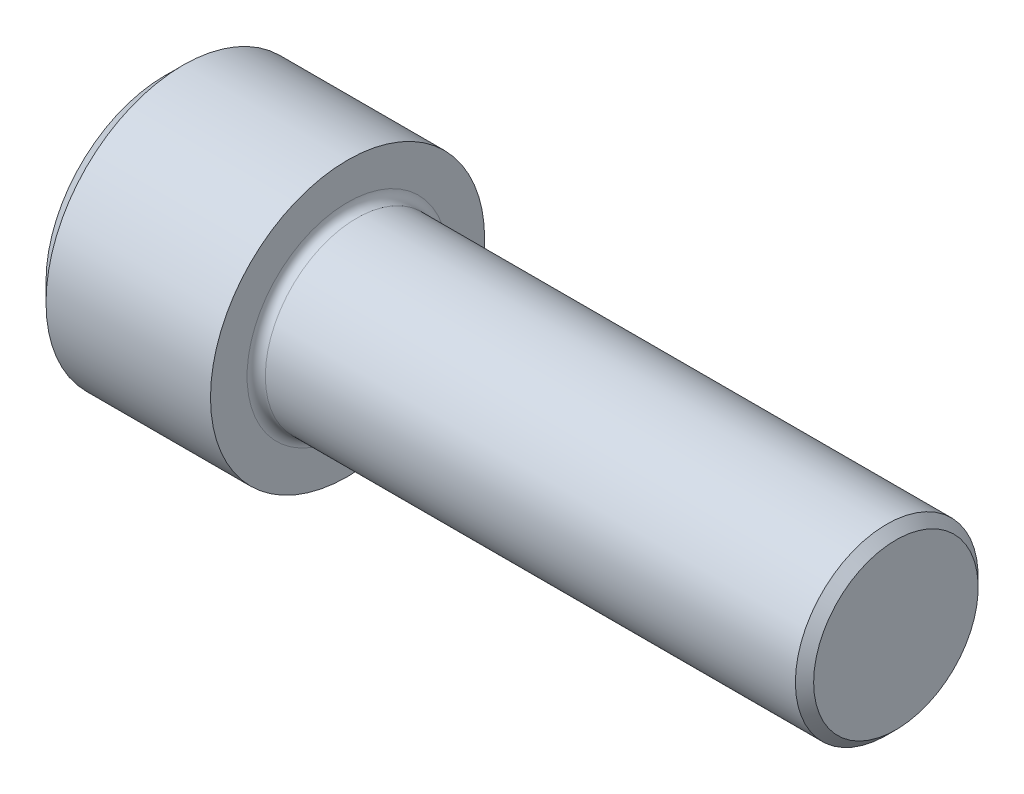
SolidWorks part; units mm, degrees
revolve "Base-Revolve" add sketch "BodySke"
sketch "BodySke" plane through (0, 0, 0) normal (0, 0, 1) x (1, 0, 0)
  line L0 (0, 0) -> (0, 16.51)
  line L1 (2.54, 19.05) -> (25.4, 19.05)
  line L2 (25.4, 19.05) -> (25.4, 12.7)
  line L3 (25.4, 12.7) -> (100.3313, 12.7)
  line L4 (101.6, 11.4313) -> (101.6, 0)
  line L5 (101.6, 0) -> (0, 0)
  line L6 (-31.75, 0) -> (127, 0) construction
  line L7 (0, 16.51) -> (2.54, 19.05)
  line L8 (101.6, 11.4313) -> (100.3313, 12.7)
  line L9 (0, -16.51) -> (2.54, -19.05) construction
  line L10 (101.6, -11.4313) -> (100.3313, -12.7) construction
  line L11 (27.5167, 9.525) -> (27.5167, 3.175) construction
  line L12 (63.5, 9.525) -> (63.5, 3.175) construction
  line L13 (63.5, 9.525) -> (63.5, 3.175) construction
  dimension "Diameter" = 25.4
  dimension "Head_ht" = 25.4
  dimension "Length" = 76.2
  dimension "Body_ch_ang" = 45
  dimension "Head_dia" = 38.1
  dimension "Head_ch_ang" = 45
  dimension "Head_side_ht" = 22.86
  dimension "Minor_dia" = 22.8625
  dimension "Advance" = 2.1167
  dimension "Thread_nom" = 38.1
  dimension "Thread_length" = 38.1
cosmetic thread "ThreadCosmetic" [suppressed]
fillet "Fillet1" radius 1.27 1 edges at (25.4, 0, 12.7)
ref_plane "Plane1" through (0, 0, 0) normal (0, 0, 1) x (1, 0, 0)
ref_plane "Plane2" through (0, 0, 0) normal (0, 1, 0) x (1, 0, 0)
ref_plane "Plane3" through (0, 0, 0) normal (1, 0, 0) x (0, 0, -1)
sketch "Sketch2" plane through (0, 0, 0) normal (0, 0, 1) x (1, 0, 0)
  line L0 (0, 9.525) -> (12.573, 9.525)
  line L1 (12.573, 9.525) -> (18.0723, 0)
  line L2 (-31.75, 0) -> (127, 0) construction
  line L3 (18.0723, 0) -> (0, 0)
  line L4 (0, 0) -> (0, 9.525)
  line L5 (0, 16.51) -> (0, -16.51) construction
  line L6 (0, 0) -> (47.625, 0) construction
  line L7 (25.4, -19.05) -> (25.4, 19.05) construction
  dimension "D2" = 60
revolve "Hex-PreBroach" cut sketch "Sketch2" angle 360 about L6
sketch "Sketch3" plane through (0, 0, 0) normal (-1, 0, 0) x (0, 0.5, 0.866)
  line L0 (5.4993, 9.525) -> (-5.4993, 9.525)
  line L1 (-5.4993, 9.525) -> (-10.9985, 0)
  line L2 (5.4993, 9.525) -> (10.9985, 0)
  line L3 (5.4993, -9.525) -> (10.9985, 0)
  line L4 (5.4993, -9.525) -> (-5.4993, -9.525)
  line L5 (-5.4993, -9.525) -> (-10.9985, 0)
extrude "Hex" cut sketch "Sketch3" against normal blind 12.573
sketch "Sketch4" plane through (0, 0, 0) normal (-1, 0, 0) x (0, 0, 1)
  line L0 (0, 0) -> (10.1727, 0)
  line L1 (0, 0) -> (6.1484, 3.5498) construction
  line L2 (0, 0) -> (5.0863, 8.8098)
  line L3 (8.4417, 2.1022) -> (9.7612, 2.864)
  line L4 (6.0414, 6.2596) -> (7.3609, 7.0215)
  arc A0 (8.4417, 2.1022) -> (6.0414, 6.2596) centre (0, 0) ccw
  arc A1 (10.1727, 0) -> (9.7612, 2.864) centre (0, 0) ccw
  arc A2 (5.0863, 8.8098) -> (7.3609, 7.0215) centre (0, 0) cw
  dimension "D1" = 30
  dimension "D2" = 60
extrude "Spline" [suppressed] cut sketch "Sketch4" against normal blind 12.573
pattern_circular "CirPattern1" [suppressed] count 6 every 60
sketch "Sketch5" plane through (0, 0, 0) normal (0, 0, 1) x (1, 0, 0)
  line L0 (-31.75, 0) -> (127, 0) construction
  line L2 (0, 16.51) -> (0, -16.51) construction
  circle A0 centre (7.874, 0) radius 1.1874
  dimension "Drilled_hole_dia" = 2.3749
  dimension "Drilled_hole_loc" = 7.874
extrude "Hole" [suppressed] cut sketch "Sketch5" against normal through all and the other way through all
pattern_circular "Drilled-4" [suppressed] count 2 every 60
pattern_circular "Drilled-6" [suppressed] count 3 every 60
sketch "ThdSchSke" plane through (0, 0, 0) normal (0, 0, 1) x (1, 0, 0)
  line L0 (63.5, -11.4313) -> (62.6116, -12.7)
  line L1 (63.5, -11.4313) -> (64.3884, -12.7)
  line L2 (64.3884, -12.7) -> (64.3884, -15.875)
  line L3 (-3.175, 0) -> (5.1513, 0) construction
  line L5 (64.3884, -15.875) -> (62.6116, -15.875)
  line L6 (62.6116, -15.875) -> (62.6116, -12.7)
  line L7 (0, 16.51) -> (0, -16.51) construction
revolve "ThreadSchematic" [suppressed] cut sketch "ThdSchSke" angle 360 about L3
pattern_linear "ThdSchPat" [suppressed]
equation "\"D2@Sketch3\" = \"Hex_size@Sketch3\" / 2"
equation "\"D1@Sketch3\" = \"Hex_size@Sketch3\" / 2"
equation "\"D1@Sketch2\" = \"Hex_size@Sketch3\" / 2"
equation "\"D3@Sketch4\" = \"Spline_p_dim@Sketch4\" / 2"
equation "\"Thread_minor@ThreadCosmetic\"  =  \"Minor_dia@BodySke\""
equation "\"D2@CirPattern1\" = 360 / \"Num_teeth@CirPattern1\""
equation "\"Wall_thickness@Sketch2\" = \"Head_ht@BodySke\" - \"Key_eng@Hex\""
equation "\"Thread_length@ThreadCosmetic\" = ((sgn( (\"Length@BodySke\" - \"Advance@BodySke\" ) - \"Thread_nom@BodySke\" )-1)*( (\"Length@BodySke\" - \"Advance@BodySke\" ) - \"Thread_nom@BodySke\" ))/-2+ \"Thread_nom@BodySke\""
equation "\"Thread_minor@ThdSchSke\" = \"Minor_dia@BodySke\""
equation "\"Diameter@ThdSchSke\" = \"Diameter@BodySke\""
equation "\"Overcut@ThdSchSke\" = \"Diameter@BodySke\" * 1.25"
equation "\"Start@ThdSchSke\" = \"Head_ht@BodySke\" + \"Length@BodySke\" - \"Thread_length@ThreadCosmetic\"  '---Non-countersunk---"
equation "\"Num_threads@ThdSchPat\" = int( \"Thread_length@ThreadCosmetic\" / \"Advance@BodySke\" + 0.999 )  + 1"
equation "\"Advance@ThdSchPat\" = \"Thread_length@ThreadCosmetic\" /  (\"Num_threads@ThdSchPat\" - 1) 'relax it"
equation "\"Num_threads@ThdSchPat\" = \"Num_threads@ThdSchPat\" - sgn( \"Num_threads@ThdSchPat\" - 1) '---chamfered tips only---"
